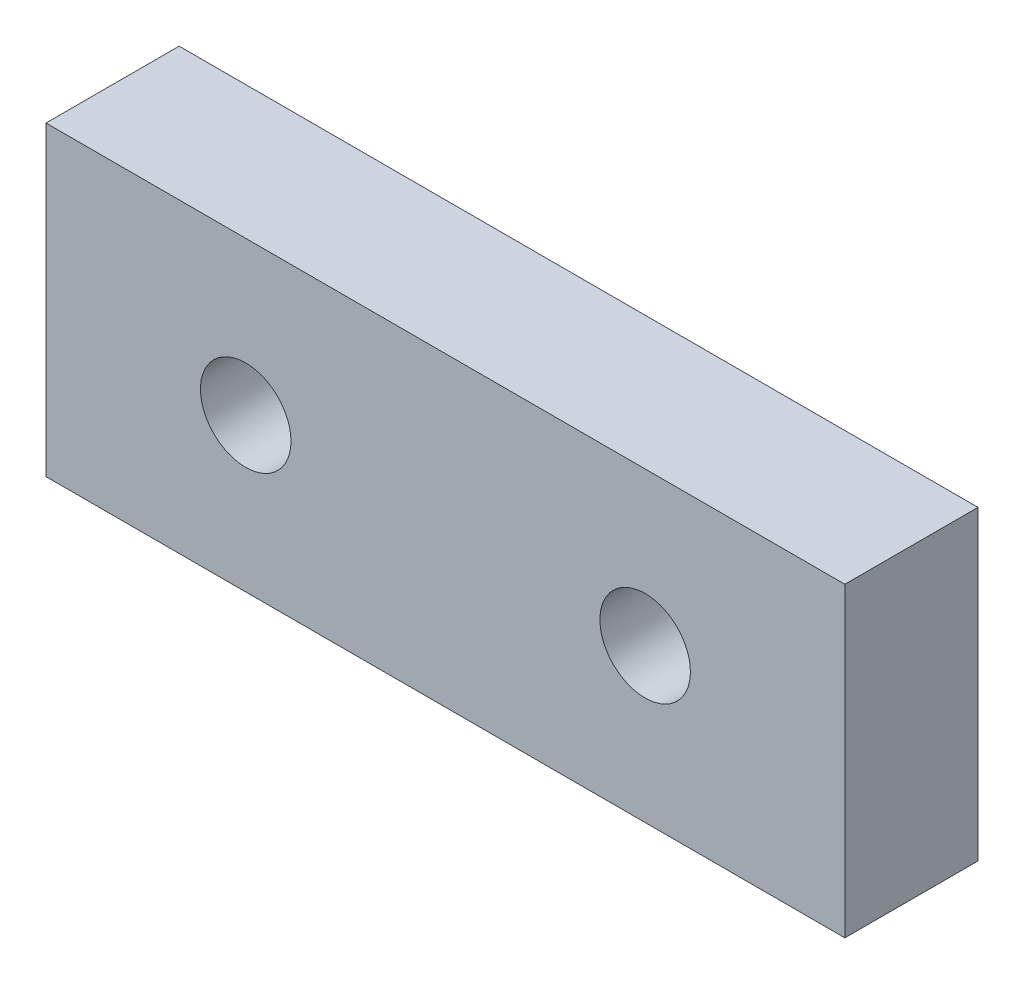
SolidWorks part; units mm, degrees
ref_plane "Front Plane" through (0, 0, 0) normal (0, 0, 1) x (1, 0, 0)
ref_plane "Top Plane" through (0, 0, 0) normal (0, 1, 0) x (1, 0, 0)
ref_plane "Right Plane" through (0, 0, 0) normal (1, 0, 0) x (0, 0, -1)
sketch "Sketch1" plane through (0, 0, 0) normal (0, 0, 1) x (1, 0, 0)
  line L1 (-15, 5.75) -> (15, 5.75)
  line L2 (-15, 5.75) -> (-15, -5.75)
  line L3 (-15, -5.75) -> (15, -5.75)
  line L4 (15, 5.75) -> (15, -5.75)
  line L5 (-15, 5.75) -> (15, -5.75) construction
  line L6 (-15, -5.75) -> (15, 5.75) construction
  point P0 (0, 0)
  dimension "D1" = 30
  dimension "D2" = 11.5
extrude "Boss-Extrude1" add sketch "Sketch1" along normal blind 5
hole_wizard "M3 Clearance Hole1" positions "Sketch4" profile "Sketch5" hole size "M3" standard "ANSI Metric" end condition through all
sketch "Sketch4" plane through (0, 0, 5) normal (0, 0, 1) x (1, 0, 0)
  line L0 (-15, 0) -> (15, 0) construction
  line L1 (-15, 5.75) -> (-15, -5.75) construction
  line L2 (15, -5.75) -> (15, 5.75) construction
  point P0 (7.5, 0)
  point P3 (-7.5, 0)
  dimension "D1" = 0
  dimension "D2" = 0
  dimension "D3" = 7.5
  dimension "D4" = 7.5
sketch "Sketch5" plane through (7.5, 0, 5) normal (1, 0, 0) x (0, -1, 0)
  line L0 (0, 0) -> (0, 5)
  line L1 (0, 5) -> (1.7, 5)
  line L2 (1.7, 5) -> (1.7, 0)
  line L5 (1.7, 0) -> (0, 0)
  line L11 (0, -6.35) -> (0, 107.95) construction
  dimension "Thru Hole Dia." = 3.4
  dimension "Thru Hole Depth" = 5
